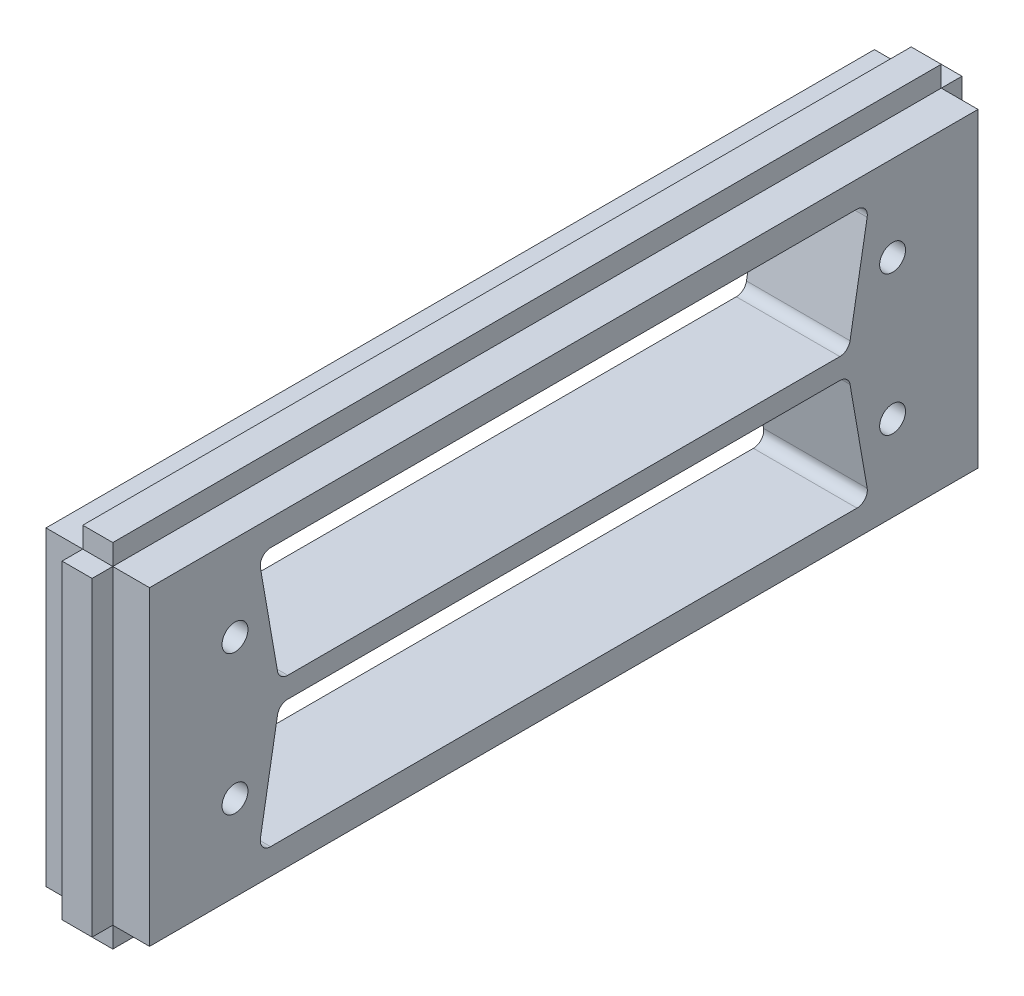
SolidWorks part; units mm, degrees
ref_plane "Front Plane" through (0, 0, 0) normal (0, 0, 1) x (1, 0, 0)
ref_plane "Top Plane" through (0, 0, 0) normal (0, 1, 0) x (1, 0, 0)
ref_plane "Right Plane" through (0, 0, 0) normal (1, 0, 0) x (0, 0, -1)
sketch "Sketch1" plane through (0, 0, 0) normal (0, 0, 1) x (1, 0, 0)
  line L0 (-5, -15) -> (-1.45, -15)
  line L1 (5, -15) -> (5, 15)
  line L2 (5, 15) -> (1.45, 15)
  line L3 (1.45, 15) -> (1.45, 17)
  line L4 (1.45, 17) -> (-1.45, 17)
  line L5 (-1.45, 17) -> (-1.45, 15)
  line L6 (-1.45, 15) -> (-5, 15)
  line L7 (-5, 15) -> (-5, -15)
  line L8 (-1.45, -15) -> (-1.45, -17)
  line L9 (-1.45, -17) -> (1.45, -17)
  line L10 (1.45, -17) -> (1.45, -15)
  line L11 (1.45, -15) -> (5, -15)
  point P9 (0, 17)
  point P14 (-5, 0)
  dimension "D1" = 10
  dimension "D2" = 2.9
  dimension "D3" = 30
  dimension "D4" = 2
  dimension "D5" = 2
extrude "MakerBeamFix" add sketch "Sketch1" along normal mid plane 80
sketch "Sketch4" plane through (-5, 0, 0) normal (-1, 0, 0) x (0, 0, 1)
  line L1 (-29.5, 12.5) -> (29.5, 12.5)
  line L2 (-29.5, 12.5) -> (-27.5, 1)
  line L3 (-27.5, 1) -> (27.5, 1)
  line L4 (29.5, 12.5) -> (27.5, 1)
  line L5 (40, 15) -> (-40, 15) construction
  circle A0 centre (-31.75, 6.75) radius 1.25
  circle A1 centre (31.75, 6.75) radius 1.25
  point P8 (-28.5, 6.75)
  point P11 (0, 1)
  dimension "D5" = 2.5
  dimension "D1" = 31.75
  dimension "D2" = 31.75
  dimension "D3" = 11.5
  dimension "D4" = 59
  dimension "D6" = 55
  dimension "D7" = 2.5
extrude "HoleForHartingConnector" cut sketch "Sketch4" against normal through all
fillet "Fillet1" radius 1 4 edges at (0, 12.5, -29.5) (0, 1, -27.5) (0, 1, 27.5) (0, 12.5, 29.5)
mirror "Mirror1" about plane through (0, 0, 0) normal (0, 1, 0) of "Fillet1", "HoleForHartingConnector"
sketch "Sketch5" plane through (0, 0, 40) normal (0, 0, 1) x (1, 0, 0)
  line L1 (-1.45, 15) -> (1.45, 15)
  line L2 (-1.45, 15) -> (-1.45, -15)
  line L3 (-1.45, -15) -> (1.45, -15)
  line L4 (1.45, 15) -> (1.45, -15)
extrude "MakerBeamFixLeft" add sketch "Sketch5" along normal blind 2
sketch "Sketch6" plane through (0, 0, -40) normal (0, 0, -1) x (-1, 0, 0)
  line L1 (-1.45, 15) -> (1.45, 15)
  line L2 (-1.45, 15) -> (-1.45, -15)
  line L3 (-1.45, -15) -> (1.45, -15)
  line L4 (1.45, 15) -> (1.45, -15)
extrude "MakerBeamFixRight" add sketch "Sketch6" along normal blind 2
